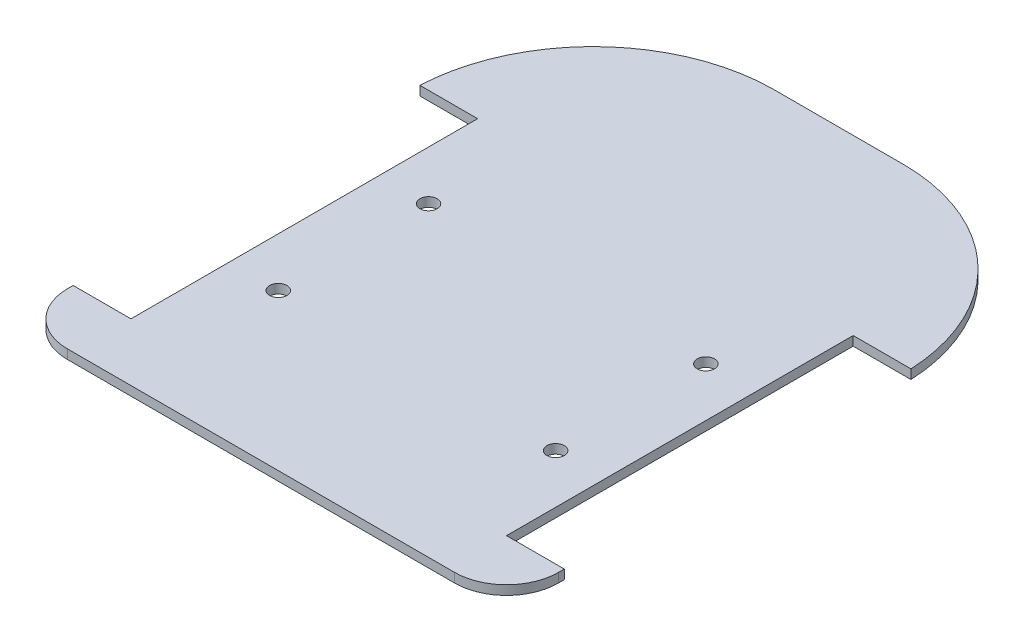
SolidWorks part; units mm, degrees
ref_plane "Front Plane" through (0, 0, 0) normal (0, 0, 1) x (1, 0, 0)
ref_plane "Top Plane" through (0, 0, 0) normal (0, 1, 0) x (1, 0, 0)
ref_plane "Right Plane" through (0, 0, 0) normal (1, 0, 0) x (0, 0, -1)
sketch "Sketch1" plane through (0, 0, 0) normal (0, 1, 0) x (1, 0, 0)
  line L0 (-45, -10) -> (45, -10) construction
  line L1 (-13.9388, 50) -> (13.9388, 50)
  line L3 (-36, -50) -> (36, -50)
  line L5 (-45, 50) -> (45, -50) construction
  line L6 (-45, -50) -> (45, 50) construction
  line L7 (-45, 20) -> (-35, 20)
  line L8 (-35, 20) -> (-35, -40)
  line L9 (-35, -40) -> (-45, -40)
  line L10 (0, -55) -> (0, 55) construction
  line L11 (35, -40) -> (45, -40)
  line L12 (35, 20) -> (35, -40)
  line L13 (45, 20) -> (35, 20)
  line L14 (-45, -40) -> (-45, -41)
  line L15 (45, -40) -> (45, -41)
  arc A0 (36, -50) -> (45, -41) centre (36, -41) ccw
  arc A1 (-45, -41) -> (-36, -50) centre (-36, -41) ccw
  arc A2 (-45, 20) -> (-13.9388, 50) centre (-13.5842, 18.5529) cw
  arc A3 (45, 20) -> (13.9388, 50) centre (13.5842, 18.5529) ccw
  point P0 (0, 0)
  point P12 (-35, -10)
  dimension "D6" = 9
  dimension "D1" = 90
  dimension "D2" = 100
  dimension "D3" = 40
  dimension "D4" = 10
  dimension "D5" = 60
extrude "Boss-Extrude1" add sketch "Sketch1" along normal blind 1.6
sketch "Sketch2" plane through (0, 1.6, 0) normal (0, 1, 0) x (1, 0, 0)
  line L0 (-35, 20) -> (-35, -40) construction
  line L1 (-45, -10) -> (45, -10) construction
  line L2 (-26.5, 3) -> (-26.5, -23) construction
  line L3 (0, -0.88) -> (0, 0.88) construction
  circle A0 centre (-26.5, 3) radius 1.5
  circle A1 centre (-26.5, -23) radius 1.5
  circle A2 centre (26.5, -23) radius 1.5
  circle A3 centre (26.5, 3) radius 1.5
  point P8 (-26.5, -10)
  dimension "D4" = 3
  dimension "D1" = 8.5
  dimension "D2" = 13
extrude "Cut-Extrude1" cut sketch "Sketch2" against normal through all
sketch "Sketch3" plane through (0, 0, 0) normal (0, 1, 0) x (1, 0, 0)
  line L1 (-2.5, -50) -> (2.5, -50)
  line L2 (-2.5, -50) -> (-2.5, 50)
  line L3 (-2.5, 50) -> (2.5, 50)
  line L4 (2.5, -50) -> (2.5, 50)
  line L5 (-2.5, -50) -> (2.5, 50) construction
  line L6 (-2.5, 50) -> (2.5, -50) construction
  point P0 (0, 0)
  dimension "D1" = 100
  dimension "D2" = 5
extrude "Cut-Extrude4" cut sketch "Sketch3" along normal up to next and the other way through all contours L1 L4 L3 L2
move or copy body "Body-Move/Copy1" bodies to move or copy 103 copy no translate (5, 0, 0)
combine bodies "Combine1" operation type add bodies to combine 104 105
